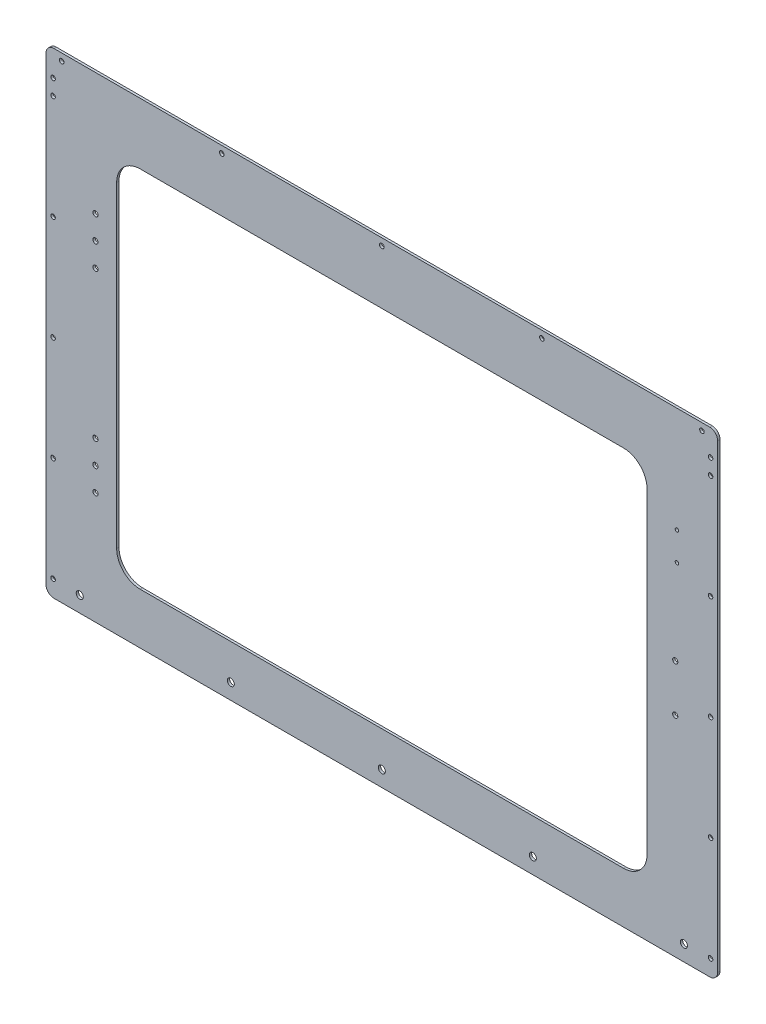
SolidWorks part; units mm, degrees
material "AISI 304"
ref_plane "Front Plane" through (0, 0, 0) normal (0, 0, 1) x (1, 0, 0)
ref_plane "Top Plane" through (0, 0, 0) normal (0, 1, 0) x (1, 0, 0)
ref_plane "Right Plane" through (0, 0, 0) normal (1, 0, 0) x (0, 0, -1)
sketch "Sketch1" plane through (0, 0, 0) normal (0, 0, 1) x (1, 0, 0)
  line L1 (0, 0) -> (856, 0)
  line L2 (0, 0) -> (0, 543.9)
  line L3 (0, 543.9) -> (856, 543.9)
  line L4 (856, 0) -> (856, 543.9)
  dimension "D1" = 856
  dimension "D2" = 543.9
extrude "MainFront" add sketch "Sketch1" along normal blind 3
sketch "Sketch2" plane through (0, 0, 3) normal (0, 0, 1) x (1, 0, 0)
  line L0 (428, 256.95) -> (428, 543.9) construction
  line L1 (90, 25) -> (766, 25)
  line L2 (90, 25) -> (90, 488.9)
  line L3 (90, 488.9) -> (766, 488.9)
  line L4 (766, 25) -> (766, 488.9)
  line L5 (90, 25) -> (766, 488.9) construction
  line L6 (90, 488.9) -> (766, 25) construction
  line L7 (856, 543.9) -> (0, 543.9) construction
  line L8 (856, 0) -> (856, 543.9) construction
  line L9 (0, 0) -> (856, 0) construction
  point P0 (428, 256.95)
  dimension "D1" = 55
  dimension "D2" = 90
  dimension "D3" = 25
extrude "DoorCut" cut sketch "Sketch2" against normal through all
fillet "DoorRoundInternal" radius 30 4 edges at (766, 25, 1.5) (90, 25, 1.5) (766, 488.9, 1.5) (90, 488.9, 1.5)
ref_plane "VerDoor" through (428, 0, 0) normal (1, 0, 0) x (0, 0, -1)
ref_plane "HorDoor" through (0, 256.95, 0) normal (0, 1, 0) x (1, 0, 0)
sketch "Sketch3" plane through (0, 0, 3) normal (0, 0, 1) x (1, 0, 0)
  line L0 (856, 0) -> (856, 543.9) construction
  line L1 (0, 0) -> (856, 0)
  line L2 (0, 0) -> (0, -40)
  line L3 (0, -40) -> (856, -40)
  line L4 (856, 0) -> (856, -40)
  dimension "D1" = 40
extrude "BottomMount" add sketch "Sketch3" against normal blind 3
hole_wizard "M8 Clearance Hole1" positions "Sketch4" profile "Sketch5" hole size "M8" standard "ISO" end condition through all
sketch "Sketch4" plane through (0, 0, 3) normal (0, 0, 1) x (1, 0, 0)
  line L0 (0, -40) -> (856, -40) construction
  line L2 (0, 543.9) -> (0, -40) construction
  point P0 (43, -20)
  dimension "D1" = 20
  dimension "D2" = 43
sketch "Sketch5" plane through (43, -20, 3) normal (1, 0, 0) x (0, -1, 0)
  line L0 (0, 0) -> (0, 3)
  line L1 (0, 3) -> (4.5, 3)
  line L2 (4.5, 3) -> (4.5, 0)
  line L5 (4.5, 0) -> (0, 0)
  line L11 (0, -6.35) -> (0, 107.95) construction
  dimension "Thru Hole Dia." = 9
  dimension "Thru Hole Depth" = 3
pattern_linear "LPattern1" count 5 spacing 192.5 along (1, 0, 0) of "M8 Clearance Hole1"
hole_wizard "M5 Clearance Hole1" positions "Sketch6" profile "Sketch8" hole size "M5" standard "ISO" end condition through all
sketch "Sketch6" plane through (0, 0, 3) normal (0, 0, 1) x (1, 0, 0)
  line L0 (0, 543.9) -> (0, -40) construction
  line L1 (0, -40) -> (856, -40) construction
  point P0 (9, -19)
  dimension "D1" = 9
  dimension "D2" = 21
sketch "Sketch8" plane through (9, -19, 3) normal (1, 0, 0) x (0, -1, 0)
  line L0 (0, 0) -> (0, 3)
  line L1 (0, 3) -> (2.9, 3)
  line L2 (2.9, 3) -> (2.9, 0)
  line L5 (2.9, 0) -> (0, 0)
  line L11 (0, -6.35) -> (0, 107.95) construction
  dimension "Thru Hole Dia." = 5.8
  dimension "Thru Hole Depth" = 3
pattern_linear "LPattern2" count 5 spacing 133.225 along (0, 1, 0) of "M5 Clearance Hole1"
mirror "Mirror1" about plane through (428, 0, 0) normal (1, 0, 0) of "LPattern2", "M5 Clearance Hole1"
hole_wizard "M5 Clearance Hole2" positions "Sketch9" profile "Sketch10" hole size "M5" standard "ISO" end condition through all
sketch "Sketch9" plane through (0, 0, 3) normal (0, 0, 1) x (1, 0, 0)
  line L0 (856, 543.9) -> (0, 543.9) construction
  line L1 (0, 543.9) -> (0, -40) construction
  point P0 (9, 533.9)
  dimension "D1" = 10
  dimension "D2" = 9
sketch "Sketch10" plane through (9, 533.9, 3) normal (1, 0, 0) x (0, -1, 0)
  line L0 (0, 0) -> (0, 3)
  line L1 (0, 3) -> (2.9, 3)
  line L2 (2.9, 3) -> (2.9, 0)
  line L5 (2.9, 0) -> (0, 0)
  line L11 (0, -6.35) -> (0, 107.95) construction
  dimension "Thru Hole Dia." = 5.8
  dimension "Thru Hole Depth" = 3
pattern_linear "LPattern3" count 2 spacing 838 along (1, 0, 0) of "M5 Clearance Hole2"
hole_wizard "M6 Clearance Hole1" positions "Sketch11" profile "Sketch12" hole size "M6" standard "ISO" end condition through all
sketch "Sketch11" plane through (0, 0, 3) normal (0, 0, 1) x (1, 0, 0)
  arc A0 (798.8, 286.95) -> (805.2, 286.95) centre (802, 286.95) ccw construction
  arc A1 (805.2, 226.95) -> (798.8, 226.95) centre (802, 226.95) ccw construction
  point P0 (802, 286.95)
  point P2 (802, 226.95)
sketch "Sketch12" plane through (802, 286.95, 3) normal (1, 0, 0) x (0, -1, 0)
  line L0 (0, 0) -> (0, 3)
  line L1 (0, 3) -> (3.3, 3)
  line L2 (3.3, 3) -> (3.3, 0)
  line L5 (3.3, 0) -> (0, 0)
  line L11 (0, -6.35) -> (0, 107.95) construction
  dimension "Thru Hole Dia." = 6.6
  dimension "Thru Hole Depth" = 3
fillet "Fillet1" radius 10 2 edges at (856, -40, 1.5) (0, -40, 1.5)
hole_wizard "M4 Clearance Hole1" positions "Sketch13" profile "Sketch14" hole size "M4" standard "ISO" end condition through all
sketch "Sketch13" plane through (0, 0, 3) normal (0, 0, 1) x (1, 0, 0)
  point P0 (804.1806, 432.409)
  point P3 (804.1806, 396.409)
sketch "Sketch14" plane through (804.1806, 432.409, 3) normal (1, 0, 0) x (0, -1, 0)
  line L0 (0, 0) -> (0, 3)
  line L1 (0, 3) -> (2.25, 3)
  line L2 (2.25, 3) -> (2.25, 0)
  line L5 (2.25, 0) -> (0, 0)
  line L11 (0, -6.35) -> (0, 107.95) construction
  dimension "Thru Hole Dia." = 4.5
  dimension "Thru Hole Depth" = 3
hole_wizard "M6 Clearance Hole2" positions "Sketch15" profile "Sketch16" hole size "M6" standard "ISO" end condition through all
sketch "Sketch15" plane through (0, 0, 3) normal (0, 0, 1) x (1, 0, 0)
  point P0 (63, 410.9)
  point P3 (63, 380.9)
  point P6 (63, 350.9)
sketch "Sketch16" plane through (63, 410.9, 3) normal (1, 0, 0) x (0, -1, 0)
  line L0 (0, 0) -> (0, 3)
  line L1 (0, 3) -> (3.3, 3)
  line L2 (3.3, 3) -> (3.3, 0)
  line L5 (3.3, 0) -> (0, 0)
  line L11 (0, -6.35) -> (0, 107.95) construction
  dimension "Thru Hole Dia." = 6.6
  dimension "Thru Hole Depth" = 3
ref_plane "Plane1" through (0, 256.95, 0) normal (0, 1, 0) x (1, 0, 0)
mirror "Mirror2" about plane through (0, 256.95, 0) normal (0, 1, 0) of "M6 Clearance Hole2"
sketch "Sketch17" plane through (0, 0, 0) normal (0, 0, -1) x (-1, 0, 0)
  line L0 (0, 543.9) -> (0, -30) construction
  line L1 (-856, 543.9) -> (0, 543.9)
  line L2 (-856, 543.9) -> (-856, 566.9)
  line L3 (-856, 566.9) -> (0, 566.9)
  line L4 (0, 543.9) -> (0, 566.9)
  dimension "D1" = 23
extrude "Boss-Extrude1" add sketch "Sketch17" against normal blind 3
hole_wizard "M5 Clearance Hole3" positions "Sketch24" profile "Sketch25" hole size "M5" standard "ISO" end condition through all
sketch "Sketch24" plane through (0, 0, 3) normal (0, 0, 1) x (1, 0, 0)
  line L0 (0, 566.9) -> (856, 566.9) construction
  line L1 (0, 566.9) -> (0, -30) construction
  point P0 (20, 557.9)
  dimension "D1" = 9
  dimension "D2" = 20
sketch "Sketch25" plane through (20, 557.9, 3) normal (1, 0, 0) x (0, -1, 0)
  line L0 (0, 0) -> (0, 3)
  line L1 (0, 3) -> (2.9, 3)
  line L2 (2.9, 3) -> (2.9, 0)
  line L5 (2.9, 0) -> (0, 0)
  line L11 (0, -6.35) -> (0, 107.95) construction
  dimension "Thru Hole Dia." = 5.8
  dimension "Thru Hole Depth" = 3
pattern_linear "LPattern4" count 5 spacing 204 along (1, 0, 0) of "M5 Clearance Hole3"
fillet "Fillet2" radius 10 2 edges at (856, 566.9, 1.5) (0, 566.9, 1.5)
